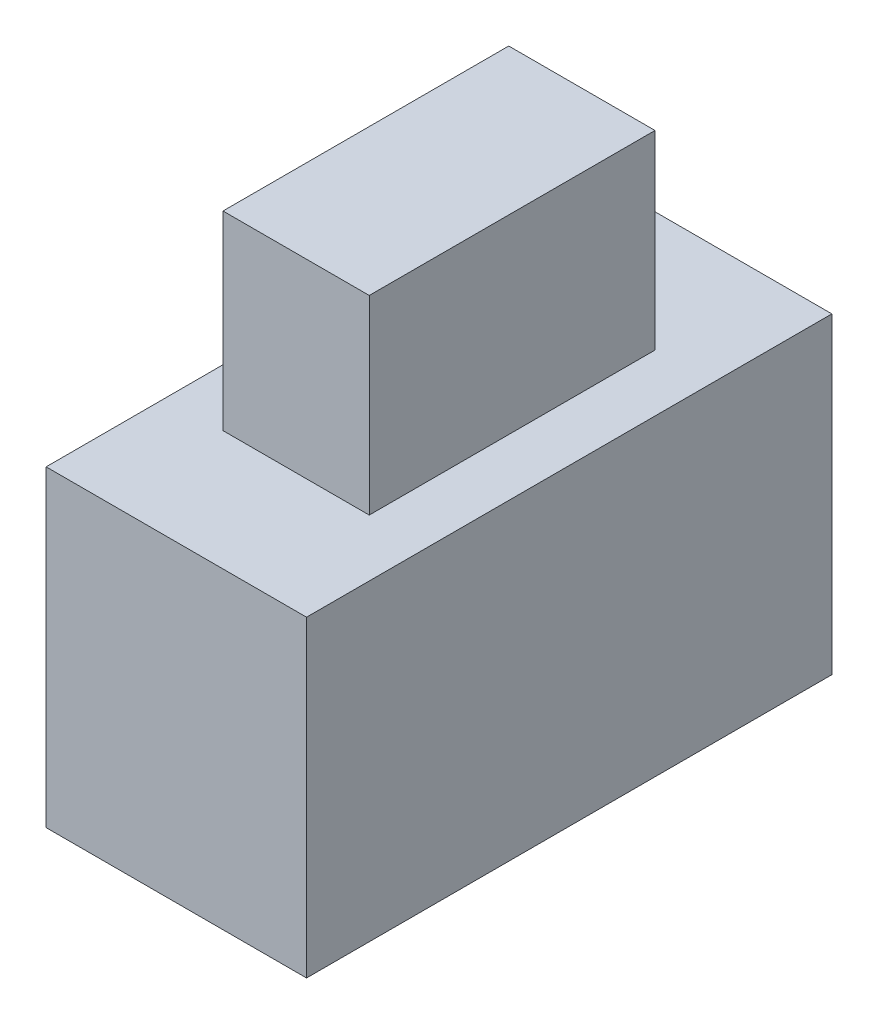
SolidWorks part; units mm, degrees
ref_plane "Front Plane" through (0, 0, 0) normal (0, 0, 1) x (1, 0, 0)
ref_plane "Top Plane" through (0, 0, 0) normal (0, 1, 0) x (1, 0, 0)
ref_plane "Right Plane" through (0, 0, 0) normal (1, 0, 0) x (0, 0, -1)
sketch "Switch Base Sketch" plane through (0, 0, 0) normal (0, 1, 0) x (1, 0, 0)
  line L1 (0, 0) -> (5.75, 0)
  line L2 (0, 0) -> (0, 11.6)
  line L3 (0, 11.6) -> (5.75, 11.6)
  line L4 (5.75, 0) -> (5.75, 11.6)
  dimension "SwitchBaseWidth" = 5.75
  dimension "SwitchBaseLength" = 11.6
extrude "Switch Base Extrude" add sketch "Switch Base Sketch" along normal blind 6.9
sketch "PullSwitch Sketch" plane through (0, 6.9, 0) normal (0, 1, 0) x (1, 0, 0)
  line L0 (2.875, 11.6) -> (2.875, 0) construction
  line L1 (5.75, 11.6) -> (0, 11.6) construction
  line L2 (0, 0) -> (5.75, 0) construction
  line L3 (0, 5.8) -> (5.75, 5.8) construction
  line L4 (0, 11.6) -> (0, 0) construction
  line L5 (5.75, 0) -> (5.75, 11.6) construction
  line L7 (1.26, 8.955) -> (4.49, 8.955)
  line L8 (1.26, 8.955) -> (1.26, 2.645)
  line L9 (1.26, 2.645) -> (4.49, 2.645)
  line L10 (4.49, 8.955) -> (4.49, 2.645)
  line L11 (1.26, 8.955) -> (4.49, 2.645) construction
  line L12 (1.26, 2.645) -> (4.49, 8.955) construction
  point P14 (2.875, 5.8)
  dimension "SwitchButtonWidth" = 3.23
  dimension "SwitchButtonLength" = 6.31
extrude "PullSwitch Extrude" add sketch "PullSwitch Sketch" along normal blind 4.2
